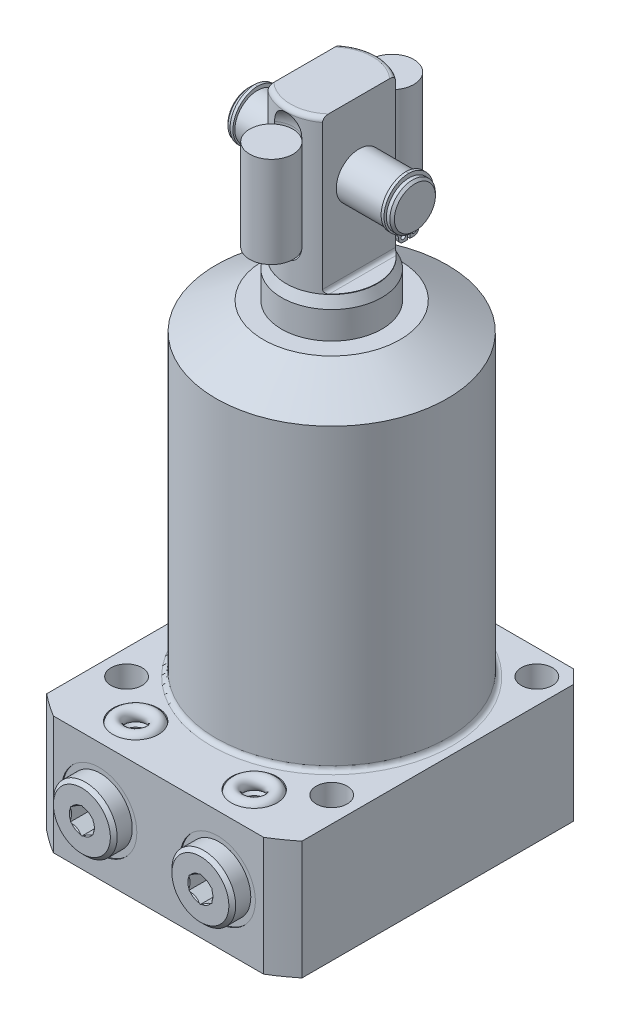
SolidWorks part; units mm, degrees
material "AISI 1020"
ref_plane "Front Plane" through (0, 0, 0) normal (0, 0, 1) x (1, 0, 0)
ref_plane "Top Plane" through (0, 0, 0) normal (0, 1, 0) x (1, 0, 0)
ref_plane "Right Plane" through (0, 0, 0) normal (1, 0, 0) x (0, 0, -1)
sketch "Sketch1" plane through (0, 0, 0) normal (0, 0, 1) x (1, 0, 0)
  line L0 (11, 0) -> (11, 77.5)
  line L1 (11, 77.5) -> (10, 79.6445)
  line L2 (10, 79.6445) -> (10, 112.25)
  line L3 (9, 113.25) -> (0, 113.25)
  line L4 (0, 61.9815) -> (0, 93.5758) construction
  line L8 (0, -3.075) -> (0, 64.575) construction
  line L9 (11, 0) -> (0, 0)
  line L10 (0, 0) -> (0, 113.25)
  line L11 (-25.0821, -26) -> (21.8096, -26) construction
  arc A0 (10, 112.25) -> (9, 113.25) centre (9, 112.25) ccw
  dimension "D1" = 1
  dimension "D2" = 22
  dimension "D3" = 20
  dimension "D4" = 35.75
  dimension "D5" = 26
  dimension "D6" = 25
  dimension "D7" = 139.25
revolve "PLUNGER" add sketch "Sketch1" angle 360 about L8
ref_plane "FLAT_SKTCH_PLN" through (0, 0, 0) normal (0, 0, 1) x (1, 0, 0)
sketch "Sketch17" plane through (0, 0, 0) normal (0, 0, 1) x (1, 0, 0)
  line L0 (9, 113.25) -> (-9, 113.25) construction
  line L1 (10, 79.6445) -> (10, 112.25) construction
  line L2 (9, 113.25) -> (-9, 113.25)
  line L3 (10, 79.6445) -> (10, 112.25)
  line L5 (6, 113.25) -> (10, 113.25)
  line L6 (6, 113.25) -> (6, 80.55)
  line L7 (6.8, 79.75) -> (10, 79.75)
  line L8 (10, 113.25) -> (10, 79.75)
  line L9 (0, 112.25) -> (0, 79.6445) construction
  line L10 (0, 57.0947) -> (0, 92.2162) construction
  line L11 (0, 77.5) -> (0, 0) construction
  line L12 (0, 77.5) -> (0, 79.6445) construction
  line L13 (-10, 113.25) -> (-10, 79.75)
  line L14 (-6.8, 79.75) -> (-10, 79.75)
  line L15 (-6, 113.25) -> (-6, 80.55)
  line L16 (-6, 113.25) -> (-10, 113.25)
  line L17 (-10, 79.6445) -> (-10, 112.25)
  arc A0 (6, 80.55) -> (6.8, 79.75) centre (6.8, 80.55) ccw
  arc A1 (-6, 80.55) -> (-6.8, 79.75) centre (-6.8, 80.55) cw
  dimension "D3" = 0.8
  dimension "D1" = 33.5
  dimension "D2" = 12
extrude "FLATS" cut sketch "Sketch17" against normal mid plane 100 contours L6 A0 L7 L8 L5 | L13 L14 A1 L15 L16
sketch "Sketch22" plane through (0, 0, 0) normal (0, 0, 1) x (1, 0, 0)
  line L0 (-11.5689, 98.25) -> (12.3381, 98.25) construction
  line L1 (0, 87.9433) -> (0, 65.5754) construction
  line L2 (0, 115.2511) -> (0, 107.7478) construction
  line L3 (0, 112.25) -> (0, 79.6445) construction
  line L4 (6, 113.25) -> (-6, 113.25) construction
  line L5 (6, 113.25) -> (-6, 113.25)
  line L6 (18.25, 102.75) -> (17.75, 103.25)
  line L7 (17.75, 103.25) -> (16.99, 103.25)
  line L8 (18.25, 102.75) -> (18.25, 98.25)
  line L9 (18.25, 98.25) -> (-18.25, 98.25)
  line L11 (16.99, 103.25) -> (16.99, 102.9365)
  line L12 (16.99, 102.9365) -> (16.25, 102.9365)
  line L13 (16.25, 102.9365) -> (16.25, 103.25)
  line L14 (16.25, 103.25) -> (-16.25, 103.25)
  line L15 (-16.25, 102.9365) -> (-16.25, 103.25)
  line L16 (-16.99, 102.9365) -> (-16.25, 102.9365)
  line L17 (-16.99, 103.25) -> (-16.99, 102.9365)
  line L18 (-18.25, 102.75) -> (-18.25, 98.25)
  line L19 (-17.75, 103.25) -> (-16.99, 103.25)
  line L20 (-18.25, 102.75) -> (-17.75, 103.25)
  dimension "D1" = 15
  dimension "D2" = 45
  dimension "D3" = 0.5
  dimension "D4" = 10
  dimension "D5" = 0.74
  dimension "D6" = 9.373
  dimension "D7" = 36.5
  dimension "D8" = 32.5
revolve "PIVOT_PIN" add sketch "Sketch22" angle 360 about L0
sketch "Sketch23" plane through (16.25, 0, 0) normal (1, 0, 0) x (0, 0, -1)
  line L0 (0, 79.466) -> (0, 70.8639) construction
  line L1 (0, 112.25) -> (0, 79.6445) construction
  line L2 (0, 98.25) -> (-3.6871, 92.5935) construction
  line L3 (-0.2765, 91.5535) -> (-1.17, 91.5535)
  line L4 (0, 98.25) -> (3.6871, 92.5935) construction
  line L5 (0.2765, 93.7635) -> (0.2765, 91.5535)
  line L6 (-0.2765, 93.7635) -> (-0.2765, 91.5535)
  line L7 (0.2765, 91.5535) -> (1.17, 91.5535)
  arc A0 (0.2765, 93.7635) -> (-0.2765, 93.7635) centre (0, 98.25) ccw
  arc A1 (-2.21, 92.5935) -> (-1.17, 91.5535) centre (-1.17, 92.5935) ccw
  arc A2 (-2.21, 92.5935) -> (-2.8805, 93.8309) centre (-3.6871, 92.5935) ccw
  arc A3 (-2.8805, 93.8309) -> (0, 104.065) centre (0.1611, 98.4972) cw
  circle A4 centre (-1.17, 92.5935) radius 0.52
  circle A5 centre (1.17, 92.5935) radius 0.52
  arc A6 (2.8805, 93.8309) -> (0, 104.065) centre (-0.1611, 98.4972) ccw
  arc A7 (2.21, 92.5935) -> (2.8805, 93.8309) centre (3.6871, 92.5935) cw
  arc A8 (2.21, 92.5935) -> (1.17, 91.5535) centre (1.17, 92.5935) cw
  point P17 (-2.4546, 94.4843)
  point P27 (2.4546, 94.4843)
  point P28 (0, 102.745)
  dimension "D1" = 8.99
  dimension "D3" = 1.04
  dimension "D8" = 1.04
  dimension "D2" = 0.553
  dimension "D4" = 2.21
  dimension "D5" = 2.21
  dimension "D6" = 1.32
  dimension "D7" = 0.78
extrude "RETAINING_RING" add sketch "Sketch23" along normal blind 0.635
ref_plane "PIN_CL" through (0, 0, 0) normal (-1, 0, 0) x (0, 0, 1)
mirror "RETAINING_RING-OPP" about plane through (0, 0, 0) normal (-1, 0, 0) of "RETAINING_RING"
sketch "Sketch20" plane through (0, 0, 0) normal (-1, 0, 0) x (0, 0, 1)
  line L0 (-6.7082, 113.25) -> (6.7082, 113.25) construction
  line L1 (-6.7082, 113.25) -> (6.7082, 113.25)
  line L2 (0, 87.5232) -> (0, 65.9324) construction
  line L3 (0, 115.2514) -> (0, 107.7471) construction
  line L4 (0, 112.25) -> (0, 79.6445) construction
  line L5 (13.2625, 85.048) -> (13.2625, 57.8595) construction
  line L6 (8.5, 108.75) -> (8.5, 87.75)
  line L7 (13.2625, 113.5125) -> (13.2625, 82.9875)
  arc A0 (13.2625, 113.5125) -> (8.5, 108.75) centre (13.2625, 108.75) ccw
  arc A1 (8.5, 87.75) -> (13.2625, 82.9875) centre (13.2625, 87.75) ccw
  dimension "D3" = 21
  dimension "D1" = 8.5
  dimension "D2" = 9.525
  dimension "D4" = 4.5
revolve "SPRING_SLOT" cut sketch "Sketch20" angle 360 about L5
mirror "SPRING_SLOT_OPP" about plane through (0, 0, 0) normal (0, 0, 1) of "SPRING_SLOT"
sketch "Sketch24" plane through (0, 0, 0) normal (-1, 0, 0) x (0, 0, 1)
  line L0 (7.2759, 98.25) -> (-10.8708, 98.25) construction
  line L1 (-13.2325, 84.5678) -> (-13.2325, 68.6953) construction
  line L2 (-8.5, 87.75) -> (-8.5, 108.75) construction
  line L3 (-8.47, 108.25) -> (-13.2325, 108.25)
  line L4 (-8.47, 108.25) -> (-8.47, 88.25)
  line L6 (-13.2325, 108.25) -> (-13.2325, 88.25)
  line L7 (-8.47, 88.25) -> (-13.2325, 88.25)
  dimension "D1" = 9.525
  dimension "D2" = 20
  dimension "D3" = 0.03
revolve "SPRING" add sketch "Sketch24" angle 360 about L1
mirror "SPRING_OPP" about plane through (0, 0, 0) normal (0, 0, 1) of "SPRING"
sketch "Sketch6" plane through (0, 0, 0) normal (0, 0, 1) x (1, 0, 0)
  line L0 (0, -26) -> (0, 67.6291) construction
  line L1 (0, 71.5) -> (15, 71.5)
  line L2 (15, 71.5) -> (25.385, 65.5042)
  line L3 (44.45, 0) -> (44.45, -26)
  line L4 (0, -26) -> (44.45, -26)
  line L5 (25.385, 0) -> (25.385, 65.5042)
  line L6 (44.45, 0) -> (25.385, 0)
  line L7 (0, -26) -> (0, 71.5)
  dimension "D1" = 50.77
  dimension "D2" = 26
  dimension "D3" = 97.5
  dimension "D4" = 88.9
  dimension "D5" = 30
  dimension "D6" = 30
revolve "BODY_REVOLVE" add sketch "Sketch6" angle 360 about L0
sketch "Sketch7" plane through (0, 0, 0) normal (0, 1, 0) x (-1, 0, 0)
  line L0 (0, 0) -> (0, -52.3237) construction
  line L1 (-28, 38) -> (28, 38)
  line L2 (-28, 38) -> (-28, -28)
  line L3 (-28, -28) -> (28, -28)
  line L4 (28, 38) -> (28, -28)
  dimension "D1" = 56
  dimension "D2" = 66
  dimension "D3" = 28
extrude "FLANGE_SIDES" cut sketch "Sketch7" against normal through all flip side to cut
sketch "Sketch8" plane through (0, -26, 0) normal (0, -1, 0) x (1, 0, 0)
  circle A0 centre (-22.5, 22.5) radius 3.4
  dimension "D1" = 6.8
  dimension "D2" = 22.5
  dimension "D3" = 22.5
extrude "MOUNTING HOLES" cut sketch "Sketch8" against normal through all
pattern_circular "MOUNTING_PATTERN" count 4 over 360 about axis through (0, 0, 0) along (0, 1, 0) of "MOUNTING HOLES"
chamfer "FLANGE_CHAMFER" distance 3 angle 45 2 edges at (-28, -13, -28) (28, -13, -28)
fillet "BODY_FILLET" radius 1 1 edges at (0, 0, -25.385)
ref_plane "FLANGE-PORT_PLANE" through (0, -13, 0) normal (0, -1, 0) x (1, 0, 0)
sketch "Sketch11" plane through (0, -13, 0) normal (0, -1, 0) x (1, 0, 0)
  line L0 (-13, 42.9716) -> (-13, 19.7499) construction
  line L1 (-21.25, 38) -> (-21.25, 37.75)
  line L3 (-21.25, 37.75) -> (-18, 37.75)
  line L4 (-18, 37.75) -> (-17.42, 37.17)
  line L5 (-17.42, 37.17) -> (-17.42, 22.59)
  line L6 (-17.42, 22.59) -> (-13, 22.59)
  line L7 (-13, 22.59) -> (-13, 38)
  line L8 (-13, 38) -> (-21.25, 38)
  line L10 (23.0608, 38) -> (-23.0608, 38) construction
  dimension "D1" = 13
  dimension "D2" = 0.25
  dimension "D3" = 8.84
  dimension "D4" = 15.16
  dimension "D5" = 16.5
  dimension "D6" = 45
  dimension "D7" = 0.58
revolve "PORT SPOT FACE" cut sketch "Sketch11" angle 360 about L0
ref_plane "MANIFOLD_PORT_PLANE" through (0, 0, 30) normal (0, 0, 1) x (1, 0, 0)
sketch "Sketch13" plane through (0, 0, 30) normal (0, 0, 1) x (1, 0, 0)
  line L0 (-15.5, -14) -> (-15.5, -23.125)
  line L1 (-15.5, -23.125) -> (-16.125, -23.75)
  line L2 (-16.125, -23.75) -> (-18, -23.75)
  line L3 (-18, -23.75) -> (-18, -26)
  line L5 (-18, -26) -> (-13, -26)
  line L6 (-13, -26) -> (-13, -14)
  line L7 (-13, -14) -> (-15.5, -14)
  line L8 (-13, 15.2099) -> (-13, -4.3918) construction
  line L10 (23.0608, -26) -> (-23.0608, -26) construction
  dimension "D1" = 13
  dimension "D2" = 5
  dimension "D3" = 12
  dimension "D4" = 2.25
  dimension "D5" = 10
  dimension "D6" = 45
  dimension "D7" = 0.625
revolve "BOTTOM_MANIFOLD_PORT" cut sketch "Sketch13" angle 360 about L8
sketch "Sketch14" plane through (0, -13, 0) normal (0, -1, 0) x (1, 0, 0)
  line L0 (-13, 32.5881) -> (-13, 43.3353) construction
  line L1 (-13, 22.59) -> (-13, 37.17) construction
  line L2 (-15.75, 41.81) -> (-19.25, 41.81)
  line L3 (-19.25, 41.81) -> (-20, 41.06)
  line L4 (-20, 41.06) -> (-20, 37.75)
  line L5 (-4.75, 37.75) -> (-21.25, 37.75) construction
  line L6 (-20, 37.75) -> (-17.125, 37.75)
  line L7 (-8, 37.75) -> (-18, 37.75) construction
  line L8 (-17.125, 37.75) -> (-17.125, 35.3078)
  line L9 (-17.125, 35.3078) -> (-13, 35.3078)
  line L10 (-13, 35.3078) -> (-13, 35.3088)
  line L11 (-13, 35.3088) -> (-15.5, 36.811)
  line L12 (-15.5, 36.811) -> (-15.5, 41.56)
  line L13 (-15.5, 41.56) -> (-15.75, 41.81)
  dimension "D1" = 8.25
  dimension "D2" = 2.4422
  dimension "D3" = 59
  dimension "D4" = 5
  dimension "D5" = 4.06
  dimension "D6" = 14
  dimension "D7" = 45
  dimension "D8" = 0.75
  dimension "D9" = 45
  dimension "D10" = 0.25
  dimension "D11" = 0.001
revolve "BSPP_PLUGHEAD" add sketch "Sketch14" angle 360 about L0
sketch "Sketch15" plane through (0, 0, 41.81) normal (0, 0, 1) x (1, 0, 0)
  line L1 (-10.5, -14.4434) -> (-10.5, -11.5566)
  line L2 (-10.5, -11.5566) -> (-13, -10.1132)
  line L3 (-13, -10.1132) -> (-15.5, -11.5566)
  line L4 (-15.5, -11.5566) -> (-15.5, -14.4434)
  line L5 (-15.5, -14.4434) -> (-13, -15.8868)
  line L6 (-13, -15.8868) -> (-10.5, -14.4434)
  circle A0 centre (-13, -13) radius 2.5 construction
  dimension "D1" = 5
extrude "BSPP_PLUG_HEX" cut sketch "Sketch15" against normal blind 4.06
mirror "MANIFOLD_TOP_MIRROR" about plane through (0, -13, 0) normal (0, -1, 0) of "BOTTOM_MANIFOLD_PORT"
mirror "BSPP-MANIFOLD_MIRROR" about plane through (0, 0, 0) normal (1, 0, 0) of "MANIFOLD_TOP_MIRROR", "PORT SPOT FACE", "BOTTOM_MANIFOLD_PORT", "BSPP_PLUGHEAD", "BSPP_PLUG_HEX"
sketch "Sketch16" plane through (0, 0, 30) normal (0, 0, 1) x (1, 0, 0)
  line L1 (-13, 9.3219) -> (-13, -15.1063) construction
  line L2 (-13, -23.125) -> (-13, -16.6451) construction
  line L3 (23.0608, -26) -> (-23.0608, -26) construction
  circle A0 centre (-16.5, -25.25) radius 1.5
  dimension "D1" = 3
  dimension "D3" = 0.75
  dimension "D2" = 7
revolve "MANIFOLD_O-RING" add sketch "Sketch16" angle 360 about L1
mirror "MANIFOLD_O-RING_MIRROR" about plane through (0, 0, 0) normal (1, 0, 0) of bodies 128
mirror "MANIFOLD_O-RING_MIRROR_TOP" about plane through (0, -13, 0) normal (0, -1, 0) of bodies 128 130
